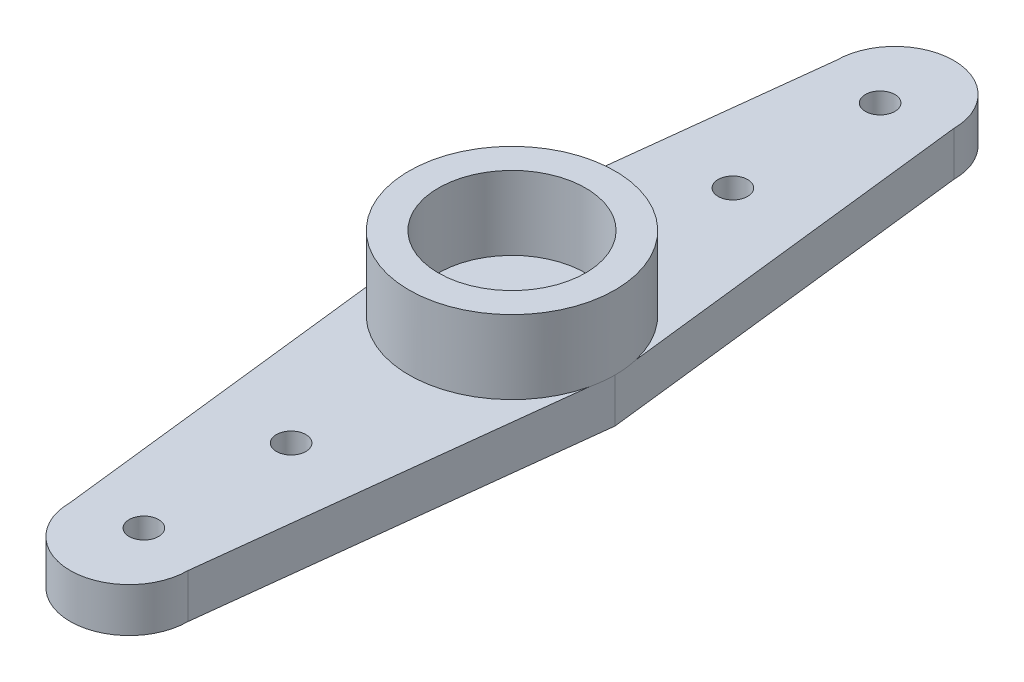
SolidWorks part; units mm, degrees
ref_plane "Спереди" through (0, 0, 0) normal (0, 0, 1) x (1, 0, 0)
ref_plane "Сверху" through (0, 0, 0) normal (0, 1, 0) x (1, 0, 0)
ref_plane "Справа" through (0, 0, 0) normal (1, 0, 0) x (0, 0, -1)
sketch "Эскиз1" plane through (0, 0, 0) normal (0, 1, 0) x (1, 0, 0)
  line L0 (-2, 13) -> (-3.5, 0)
  line L1 (-3.5, 0) -> (3.5, 0) construction
  line L2 (-2, -13) -> (-3.5, 0)
  line L3 (3.5, 0) -> (2, 13)
  line L4 (3.5, 0) -> (2, -13)
  circle A0 centre (0, 0) radius 3.5
  circle A1 centre (0, 13) radius 2
  circle A2 centre (0, -13) radius 2
  dimension "D1" = 7
  dimension "D2" = 4
  dimension "D6" = 13
extrude "Бобышка-Вытянуть2" add sketch "Эскиз1" along normal blind 1.5 contours A1 | A1 L0 A0 L3 | L3 A0 L0 | L1 L2 A0 L4 | L2 A2 L4 A0 | A2
sketch "Эскиз7" plane through (0, 1.5, 0) normal (0, 1, 0) x (1, 0, 0)
  circle A0 centre (0, 0) radius 3.5
  dimension "D1" = 7
extrude "Бобышка-Вытянуть3" add sketch "Эскиз7" along normal blind 2.5
sketch "Эскиз8" plane through (0, 4, 0) normal (0, 1, 0) x (1, 0, 0)
  circle A0 centre (0, 0) radius 2.5
  dimension "D1" = 5
extrude "Вырез-Вытянуть1" cut sketch "Эскиз8" against normal blind 2.5
sketch "Эскиз9" plane through (0, 0, 0) normal (0, -1, 0) x (1, 0, 0)
  circle A0 centre (0, 0) radius 2.25
  dimension "D1" = 4.5
extrude "Вырез-Вытянуть2" cut sketch "Эскиз9" against normal blind 0.5
sketch "Эскиз10" plane through (0, 0.5, 0) normal (0, -1, 0) x (1, 0, 0)
  circle A0 centre (0, 0) radius 0.9
  dimension "D1" = 1.8
extrude "Вырез-Вытянуть3" cut sketch "Эскиз10" against normal blind 1
sketch "Эскиз11" plane through (0, 0, 0) normal (0, -1, 0) x (1, 0, 0)
  line L0 (-3.5, 0) -> (3.5, 0) construction
  circle A0 centre (0, -7.5) radius 0.5
  circle A1 centre (0, 0) radius 3.5 construction
  circle A2 centre (0, -12.5) radius 0.5
  circle A4 centre (0, 12.5) radius 0.5
  circle A5 centre (0, 7.5) radius 0.5
  dimension "D1" = 1
  dimension "D3" = 12.5
  dimension "D2" = 7.5
extrude "Вырез-Вытянуть4" cut sketch "Эскиз11" against normal blind 1.5
